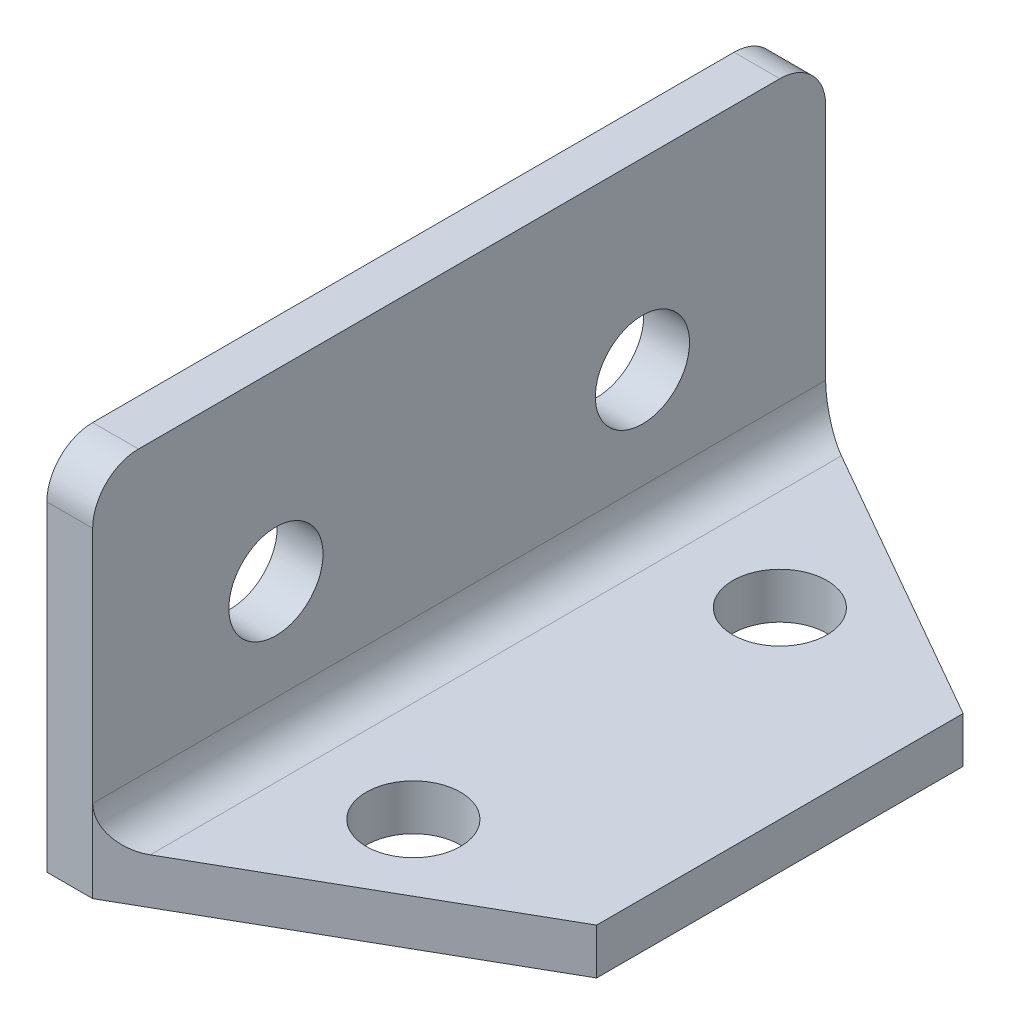
SolidWorks part; units mm, degrees
material "3003 Alloy"
ref_plane "Front Plane" through (0, 0, 0) normal (0, 0, 1) x (1, 0, 0)
ref_plane "Top Plane" through (0, 0, 0) normal (0, 1, 0) x (1, 0, 0)
ref_plane "Right Plane" through (0, 0, 0) normal (1, 0, 0) x (0, 0, -1)
sketch "Sketch1" plane through (0, 0, 0) normal (0, 1, 0) x (1, 0, 0)
  line L0 (12.7, -949.2) -> (12.7, 49050.8) construction
  line L1 (0, 0) -> (25.4, 0)
  line L2 (0, 0) -> (0, 50.8)
  line L3 (0, 50.8) -> (25.4, 50.8)
  line L4 (25.4, 0) -> (25.4, 50.8)
  circle A0 centre (12.7, 38.1) radius 3.2639
  circle A1 centre (12.7, 12.7) radius 3.2639
  point P6 (12.7, 38.1)
  point P8 (12.7, 50.8)
  point P9 (12.7, 12.7)
  dimension "D5" = 6.5278
  dimension "D6" = 6.5278
  dimension "D1" = 50.8
  dimension "D2" = 25.4
  dimension "D3" = 12.7
  dimension "D4" = 12.7
extrude "Boss-Extrude1" add sketch "Sketch1" along normal blind 3.175
sketch "Sketch2" plane through (0, 3.175, 0) normal (0, 1, 0) x (1, 0, 0)
  line L0 (25.4, 50.8) -> (0, 50.8) construction
  line L1 (0, 0) -> (3.175, 0)
  line L2 (0, 0) -> (0, 50.8)
  line L3 (0, 50.8) -> (3.175, 50.8)
  line L4 (3.175, 0) -> (3.175, 50.8)
  dimension "D1" = 3.175
extrude "Boss-Extrude2" add sketch "Sketch2" along normal blind 22.225
sketch "Sketch3" plane through (3.175, 0, 0) normal (1, 0, 0) x (0, 0, -1)
  line L0 (25.4, 25.4) -> (25.4, 12.7) construction
  line L1 (0, 25.4) -> (50.8, 25.4) construction
  line L2 (25.4, 12.7) -> (12.7, 12.7) construction
  line L3 (25.4, 12.7) -> (38.1, 12.7) construction
  circle A0 centre (12.7, 12.7) radius 3.2639
  circle A1 centre (38.1, 12.7) radius 3.2639
  dimension "D4" = 6.5278
  dimension "D5" = 6.5278
  dimension "D1" = 12.7
  dimension "D2" = 12.7
  dimension "D3" = 12.7
extrude "Cut-Extrude1" cut sketch "Sketch3" against normal blind 22.225
fillet "Fillet2" radius 2.54 1 edges at (3.175, 3.175, -25.4)
sketch "Sketch4" plane through (0, 3.175, 0) normal (0, 1, 0) x (1, 0, 0)
  line L0 (25.4, 0) -> (25.4, 12.7)
  line L1 (25.4, 0) -> (25.4, 50.8) construction
  line L2 (25.4, 0) -> (3.175, 0)
  line L3 (5.715, 0) -> (25.4, 0) construction
  line L4 (3.175, 0) -> (25.4, 12.7)
  line L5 (-994.285, 25.4) -> (49005.715, 25.4) construction
  line L6 (5.715, 50.8) -> (5.715, 0) construction
  line L7 (25.4, 50.8) -> (25.4, 38.1)
  line L8 (25.4, 50.8) -> (3.175, 50.8)
  line L9 (3.175, 50.8) -> (25.4, 38.1)
  point P13 (5.715, 25.4)
  dimension "D1" = 12.7
  dimension "D2" = 22.225
extrude "Cut-Extrude3" cut sketch "Sketch4" against normal through all both and the other way through all
fillet "Fillet3" radius 3.175 1 edges at (1.5875, 25.4, 0)
fillet "Fillet4" radius 3.175 1 edges at (1.5875, 25.4, -50.8)
